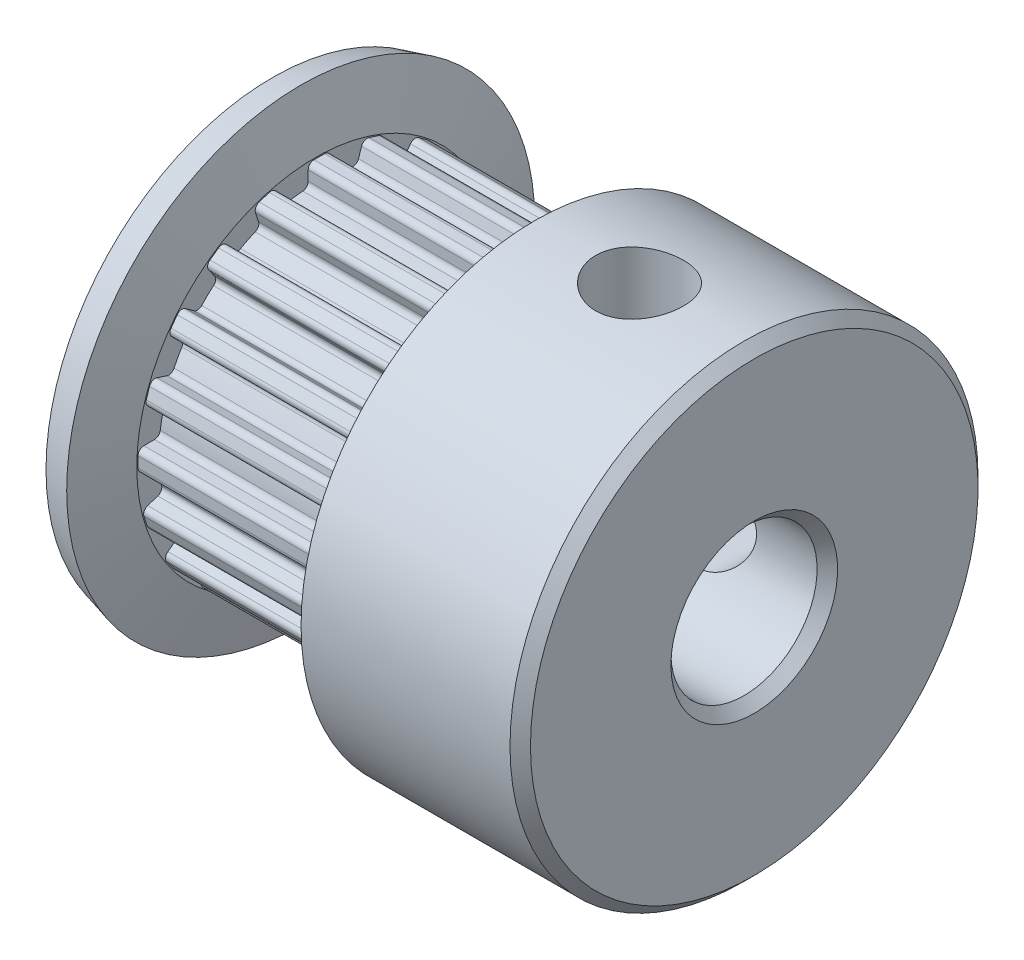
SolidWorks part; units mm, degrees
material "2024-T4"
ref_plane "Front Plane" through (0, 0, 0) normal (0, 0, 1) x (1, 0, 0)
ref_plane "Top Plane" through (0, 0, 0) normal (0, 1, 0) x (1, 0, 0)
ref_plane "Right Plane" through (0, 0, 0) normal (1, 0, 0) x (0, 0, -1)
sketch "Sketch1" plane through (0, 0, 0) normal (0, 0, 1) x (1, 0, 0)
  line L0 (-7.0776, 0) -> (8.2224, 0)
  line L1 (8.5724, 0.35) -> (8.5724, 5.15)
  line L2 (8.2224, 5.5) -> (1.0788, 5.5)
  line L3 (0.5724, 3.61) -> (0.5724, 2.85)
  line L4 (0.5724, 2.85) -> (-6.4276, 2.85)
  line L5 (-7.4276, 2.85) -> (-7.4276, 0.35)
  line L6 (-7.4276, -2.5) -> (8.5724, -2.5) construction
  line L7 (-8.4276, 2.85) -> (-8.4276, -12.6573) construction
  line L8 (-8.4276, 2.85) -> (-8.4276, 0) construction
  line L9 (0.5724, 5.5) -> (-12.4584, 5.5) construction
  line L10 (0.5724, 3.61) -> (-7.4276, 3.61) construction
  line L11 (-6.4276, 2.85) -> (-6.4276, 3.61)
  line L12 (-6.4276, 3.61) -> (-6.9341, 5.5)
  line L13 (-7.4276, 2.85) -> (-7.4276, 3.4783)
  line L14 (-7.4276, 3.4783) -> (-7.9, 5.2412)
  line L15 (-7.9, 5.2412) -> (-6.9341, 5.5)
  line L16 (-7.4276, 0) -> (8.5724, 0) construction
  line L17 (8.2224, 0) -> (8.5724, 0.35)
  line L18 (-7.4276, 2.85) -> (-7.4276, 0) construction
  line L19 (-7.4276, 0.35) -> (-7.0776, 0)
  line L20 (8.5724, 5.15) -> (8.2224, 5.5)
  line L21 (0.5724, 2.85) -> (-7.4276, 2.85) construction
  line L22 (1.0788, 5.5) -> (0.5724, 3.61)
  point P4 (8.5724, 5.5)
  dimension "D2" = 8
  dimension "D3" = 2.5
  dimension "D4" = 8
  dimension "D5" = 5.35
  dimension "D8" = 1
  dimension "D9" = 195
  dimension "D11" = 1.89
  dimension "D12" = 15
  dimension "D6" = 1
  dimension "D7" = 0.76
  dimension "D10" = 1
revolve "Revolve2" add sketch "Sketch1" angle 360 about L6
sketch "Sketch2" plane through (0.5724, 0, 0) normal (-1, 0, 0) x (0, 0, 1)
  line L1 (-0.51, 2.8066) -> (0.25, 2.8066)
  line L2 (-0.51, 2.8066) -> (-0.51, 3.5666)
  line L3 (-0.51, 3.5666) -> (0.25, 3.5666)
  line L4 (0.25, 2.8066) -> (0.25, 3.5666)
  dimension "D1" = 0.76
  dimension "D2" = 0.76
extrude "Boss-Extrude1" add sketch "Sketch2" along normal up to surface (7 mm away) up to face at (-6.4276, -2.5, 6.11)
fillet "Fillet1" radius 0.2 4 edges at (-2.9276, 2.8256, -0.51) (-2.9276, 2.8442, 0.25) (-2.9276, 3.5666, -0.51) (-2.9276, 3.5666, 0.25)
pattern_circular "CirPattern2" count 20 over 360 about axis through (0, -2.5, 0) along (1, 0, 0) of "Boss-Extrude1", "Fillet1"
sketch "Sketch3" plane through (0, 0, 0) normal (0, 1, 0) x (1, 0, 0)
  line L0 (1.0788, -8) -> (8.2224, -8) construction
  line L3 (4.6506, -8) -> (4.6506, 8) construction
  line L4 (8.2224, 8) -> (1.0788, 8) construction
  circle A0 centre (4.6506, 0) radius 1.5
extrude "Cut-Extrude2" cut sketch "Sketch3" against normal blind 3 and the other way blind 9 contours A0
pattern_circular "CirPattern3" count 2 every 90 about axis through (-7.4276, -2.5, 0) along (-1, 0, 0) of "Cut-Extrude2"
